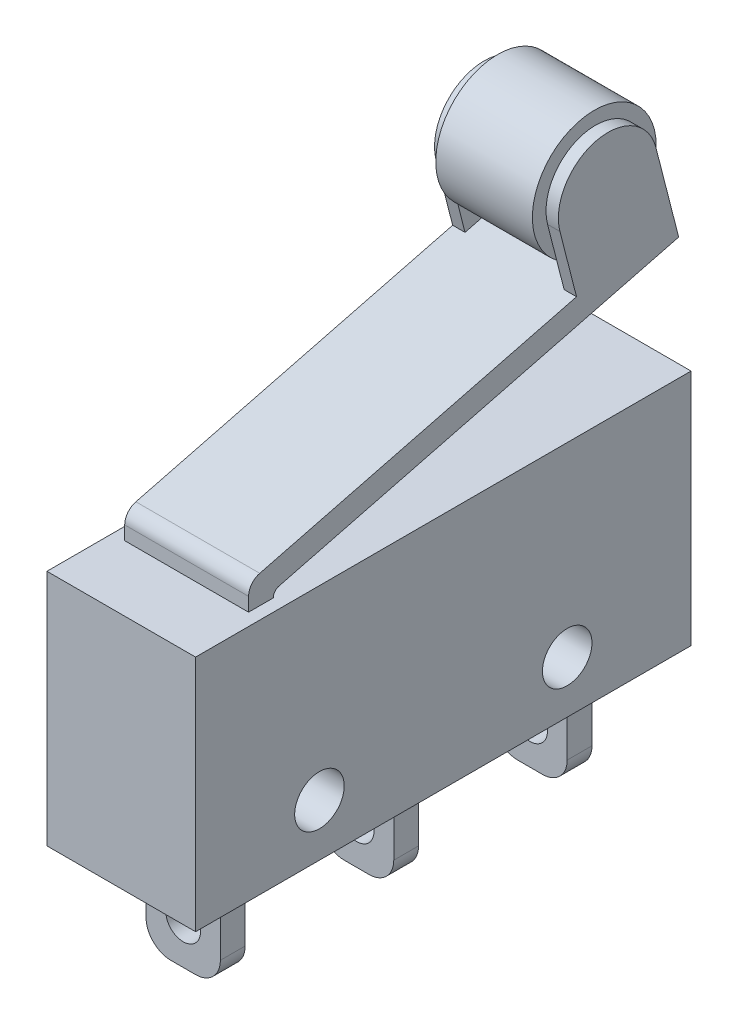
SolidWorks part; units mm, degrees
ref_plane "Front Plane" through (0, 0, 0) normal (0, 0, 1) x (1, 0, 0)
ref_plane "Top Plane" through (0, 0, 0) normal (0, 1, 0) x (1, 0, 0)
ref_plane "Right Plane" through (0, 0, 0) normal (1, 0, 0) x (0, 0, -1)
sketch "Sketch1" plane through (0, 0, 0) normal (1, 0, 0) x (0, 0, -1)
  line L0 (-6.9099, 5.934) -> (9.752, 10.2)
  line L1 (10, -4.8) -> (-10, -4.8)
  line L2 (10, -4.8) -> (10, 4.8)
  line L3 (10, 4.8) -> (-10, 4.8)
  line L4 (-10, -4.8) -> (-10, 4.8)
  line L5 (0, 4.8) -> (0, -4.8) construction
  line L6 (10, 0) -> (-10, 0) construction
  line L7 (9.752, 10.2) -> (10, 9.2312)
  line L8 (10, 9.2312) -> (-6.1355, 5.1)
  line L9 (9.752, 10.2) -> (9.0823, 12.8156)
  line L10 (-6.5, -4.8) -> (-7.5, -4.8)
  line L11 (-6.5, -4.8) -> (-6.5, -8.8)
  line L12 (-6.5, -8.8) -> (-7.5, -8.8)
  line L13 (-7.5, -4.8) -> (-7.5, -8.8)
  line L14 (-7, -8.8) -> (-7, -4.8) construction
  line L15 (-6.5, -6.8) -> (-7.5, -6.8) construction
  line L16 (0.5, -4.8) -> (-0.5, -4.8)
  line L17 (0.5, -4.8) -> (0.5, -8.8)
  line L18 (0.5, -8.8) -> (-0.5, -8.8)
  line L19 (-0.5, -4.8) -> (-0.5, -8.8)
  line L20 (0, -8.8) -> (0, -4.8) construction
  line L21 (0.5, -6.8) -> (-0.5, -6.8) construction
  line L22 (7.5, -4.8) -> (6.5, -4.8)
  line L23 (7.5, -4.8) -> (7.5, -8.8)
  line L24 (7.5, -8.8) -> (6.5, -8.8)
  line L25 (6.5, -4.8) -> (6.5, -8.8)
  line L26 (7, -8.8) -> (7, -4.8) construction
  line L27 (7.5, -6.8) -> (6.5, -6.8) construction
  line L28 (5.2073, 11.8235) -> (5.877, 9.2079)
  line L29 (-6.3611, 4.8) -> (-6.3611, 4.8093)
  line L30 (-7.3611, 4.8) -> (-7.3611, 5.3527)
  line L31 (-7.3611, 4.8) -> (-7.3611, 5.0422) construction
  line L32 (-6.3611, 4.8) -> (-6.3611, 5.0422) construction
  arc A0 (9.0823, 12.8156) -> (5.2073, 11.8235) centre (7.1448, 12.3196) ccw
  circle A1 centre (7.1448, 12.3196) radius 2.5 construction
  arc A2 (-6.9099, 5.934) -> (-7.3611, 5.3527) centre (-6.7611, 5.3527) ccw
  arc A3 (-6.3611, 4.8093) -> (-6.1355, 5.1) centre (-6.0611, 4.8093) cw
  point P0 (0, 0)
  point P69 (-7, -6.8)
  point P92 (7, -6.8)
  point P112 (0, -6.8)
  dimension "D4" = 5
  dimension "D12" = 0.6
  dimension "D13" = 0.3
  dimension "D1" = 9.6
  dimension "D2" = 20
  dimension "D3" = 1
  dimension "D5" = 15
  dimension "D6" = 1
  dimension "D7" = 4
  dimension "D8" = 6
  dimension "D9" = 2.7
  dimension "D10" = 4
  dimension "D11" = 1
extrude "Boss-Extrude1" add sketch "Sketch1" along normal mid plane 6
sketch "Sketch2" plane through (3, 0, 0) normal (1, 0, 0) x (0, 0, -1)
  line L0 (0, 0) -> (0, -9.3659) construction
  line L1 (10, 4.8) -> (-6.3611, 4.8) construction
  circle A0 centre (-5, -2.7) radius 1
  circle A1 centre (5, -2.7) radius 1
  dimension "D1" = 2
  dimension "D2" = 7.5
  dimension "D3" = 10
extrude "Cut-Extrude1" cut sketch "Sketch2" against normal blind 6
sketch "Sketch4" plane through (0, 0, 7.5) normal (0, 0, 1) x (1, 0, 0)
  line L0 (0, 0) -> (0, -8.8) construction
  line L1 (3, -8.8) -> (-3, -8.8) construction
  line L2 (3, -4.8) -> (-3, -4.8) construction
  line L3 (3, -8.8) -> (1.5, -8.8)
  line L4 (3, -8.8) -> (3, -4.8)
  line L5 (3, -4.8) -> (1.5, -4.8)
  line L6 (1.5, -8.8) -> (1.5, -4.8)
  line L7 (2.25, -4.8) -> (2.25, -8.8) construction
  line L8 (3, -6.8) -> (1.5, -6.8) construction
  line L9 (-3, -6.8) -> (-1.5, -6.8) construction
  line L10 (-2.25, -4.8) -> (-2.25, -8.8) construction
  line L11 (-1.5, -8.8) -> (-1.5, -4.8)
  line L12 (-3, -4.8) -> (-1.5, -4.8)
  line L13 (-3, -8.8) -> (-3, -4.8)
  line L14 (-3, -8.8) -> (-1.5, -8.8)
  line L15 (0, -7.2) -> (0, -6.4) construction
  line L16 (-0.7, -7.2) -> (-0.7, -6.4)
  line L17 (0.7, -7.2) -> (0.7, -6.4)
  arc A0 (-0.7, -7.2) -> (0.7, -7.2) centre (0, -7.2) ccw
  arc A1 (0.7, -6.4) -> (-0.7, -6.4) centre (0, -6.4) ccw
  point P19 (-2.25, -6.8)
  point P22 (0, -6.8)
  point P81 (2.25, -6.8)
  dimension "D3" = 0.7
  dimension "D1" = 3
  dimension "D2" = 0.8
extrude "Cut-Extrude2" cut sketch "Sketch4" against normal through all
sketch "Sketch5" plane through (3, 0, 0) normal (1, 0, 0) x (0, 0, -1)
  line L0 (-6.3611, 4.8) -> (-7.3611, 4.8)
  line L8 (-10, 4.8) -> (-10, -4.8)
  line L9 (-10, -4.8) -> (10, -4.8)
  line L10 (10, -4.8) -> (10, 4.8)
  line L11 (10, 4.8) -> (-6.3611, 4.8)
  line L12 (-6.1355, 5.1) -> (10, 9.2312)
  line L13 (10, 9.2312) -> (9.0823, 12.8156)
  line L14 (5.2073, 11.8235) -> (5.877, 9.2079)
  line L15 (5.877, 9.2079) -> (-6.9099, 5.934)
  line L20 (-6.1355, 5.1) -> (10, 9.2312)
  line L21 (10, 9.2312) -> (9.0823, 12.8156)
  line L22 (5.2073, 11.8235) -> (5.877, 9.2079)
  line L23 (5.877, 9.2079) -> (-6.9099, 5.934)
  line L24 (-6.3611, 4.8) -> (-6.3611, 4.8093)
  line L25 (-6.3611, 4.8) -> (-6.3611, 4.8093)
  line L26 (-7.3611, 5.3527) -> (-7.3611, 4.8)
  line L27 (-7.3611, 5.3527) -> (-7.3611, 4.8)
  line L28 (-7.3611, 4.8) -> (-10, 4.8)
  arc A1 (9.0823, 12.8156) -> (5.2073, 11.8235) centre (7.1448, 12.3196) ccw
  arc A2 (9.0823, 12.8156) -> (5.2073, 11.8235) centre (7.1448, 12.3196) ccw
  arc A5 (-6.1355, 5.1) -> (-6.3611, 4.8093) centre (-6.0611, 4.8093) ccw
  arc A6 (-6.1355, 5.1) -> (-6.3611, 4.8093) centre (-6.0611, 4.8093) ccw
  arc A7 (-6.9099, 5.934) -> (-7.3611, 5.3527) centre (-6.7611, 5.3527) ccw
  arc A8 (-6.9099, 5.934) -> (-7.3611, 5.3527) centre (-6.7611, 5.3527) ccw
  dimension "D1" = 0
extrude "Cut-Extrude3" cut sketch "Sketch5" against normal blind 0.5
mirror "Mirror1" about plane through (0, 0, 0) normal (1, 0, 0) of "Cut-Extrude3"
sketch "Sketch6" plane through (0, 1.9786, -7.7279) normal (0, -0.248, 0.9688) x (1, 0, 0)
  line L0 (0, 0) -> (0, 14.158) construction
  line L1 (2.5, 12.1624) -> (-2.5, 12.1624) construction
  line L2 (2, 12.1624) -> (-2, 12.1624)
  line L3 (2, 12.1624) -> (2, 7.4624)
  line L4 (2, 7.4624) -> (-2, 7.4624)
  line L5 (-2, 12.1624) -> (-2, 7.4624)
  line L6 (0, 7.4624) -> (0, 12.1624) construction
  line L7 (2, 9.8124) -> (-2, 9.8124) construction
  line L8 (2.5, 7.4624) -> (-2.5, 7.4624) construction
  line L9 (-2.5, 12.1624) -> (-2.5, 10.1624) construction
  point P55 (0, 9.8124)
  dimension "D1" = 0.5
extrude "Cut-Extrude4" cut sketch "Sketch6" against normal through all
sketch "Sketch7" plane through (0, 0, 0) normal (1, 0, 0) x (0, 0, -1)
  circle A0 centre (7.1448, 12.3196) radius 2.5
  dimension "D1" = 5
extrude "Boss-Extrude2" add sketch "Sketch7" along normal mid plane 3.9 separate body
fillet "Fillet1" radius 1 6 edges at (-1.5, -8.8, 0) (-1.5, -8.8, -7) (-1.5, -8.8, 7) (1.5, -8.8, -7) (1.5, -8.8, 0) (1.5, -8.8, 7)
